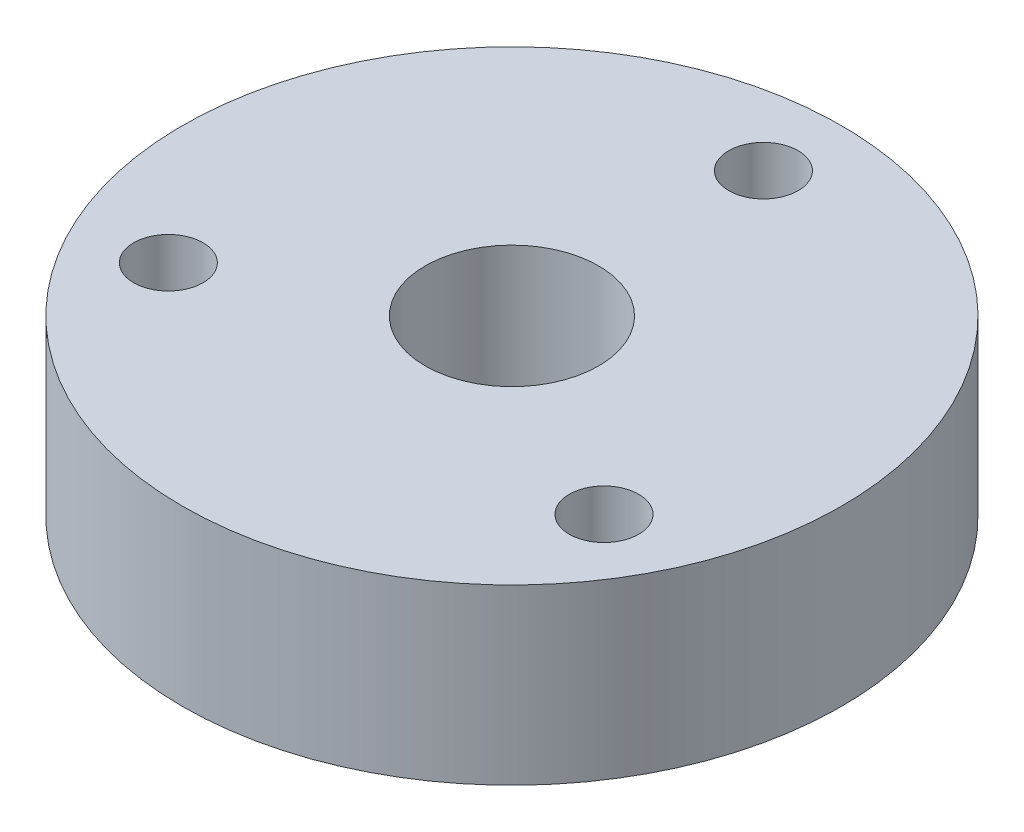
SolidWorks part; units mm, degrees
ref_plane "Front Plane" through (0, 0, 0) normal (0, 0, 1) x (1, 0, 0)
ref_plane "Top Plane" through (0, 0, 0) normal (0, 1, 0) x (1, 0, 0)
ref_plane "Right Plane" through (0, 0, 0) normal (1, 0, 0) x (0, 0, -1)
sketch "Sketch1" plane through (0, 0, 0) normal (0, 1, 0) x (1, 0, 0)
  circle A0 centre (0, 0) radius 19
  circle A3 centre (0, 0) radius 14.5 construction
  circle A4 centre (0, 14.5) radius 2
  circle A5 centre (12.5574, -7.25) radius 2
  circle A6 centre (-12.5574, -7.25) radius 2
  circle A7 centre (0, 0) radius 5
  point P13 (0, 0)
  dimension "D1" = 3
  dimension "D3" = 38
extrude "Boss-Extrude1" add sketch "Sketch1" along normal blind 10
